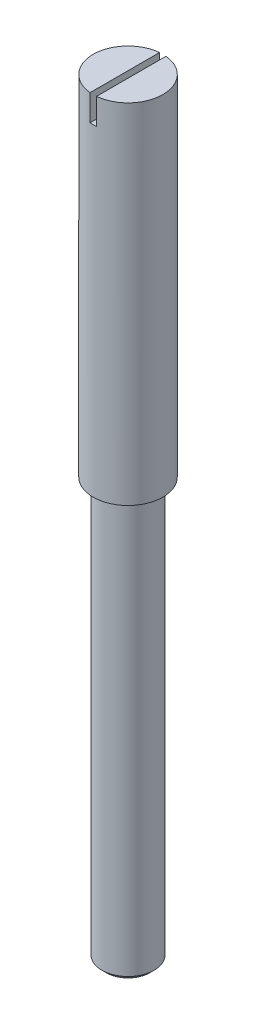
SolidWorks part; units mm, degrees
material "Plain Carbon Steel"
ref_plane "Front Plane" through (0, 0, 0) normal (0, 0, 1) x (1, 0, 0)
ref_plane "Top Plane" through (0, 0, 0) normal (0, 1, 0) x (1, 0, 0)
ref_plane "Right Plane" through (0, 0, 0) normal (1, 0, 0) x (0, 0, -1)
sketch "Sketch1" plane through (0, 0, 0) normal (0, 0, 1) x (1, 0, 0)
  line L0 (0, -1.4901) -> (0, 11.5997) construction
  line L1 (0, 0) -> (0.375, 0)
  line L2 (0.375, 0) -> (0.375, 6)
  line L3 (0.375, 6) -> (0.5, 6)
  line L4 (0.5, 6) -> (0.5, 11)
  line L5 (0.5, 11) -> (0, 11)
  line L6 (0, 0) -> (0, 11)
  dimension "D1" = 11
  dimension "D2" = 5
  dimension "D3" = 0.375
  dimension "D4" = 0.5
revolve "Revolve1" add sketch "Sketch1" angle 360 about L0
sketch "Sketch2" plane through (0, 0, 0) normal (0, 0, 1) x (1, 0, 0)
  line L0 (0.5, 11) -> (-0.5, 11) construction
  line L1 (-0.0465, 11.3483) -> (0.0465, 11.3483)
  line L2 (-0.0465, 11.3483) -> (-0.0465, 10.6257)
  line L3 (-0.0465, 10.6257) -> (0.0465, 10.6257)
  line L4 (0.0465, 11.3483) -> (0.0465, 10.6257)
  point P4 (0, 10.6257)
  dimension "D1" = 0.093
  dimension "D2" = 0.3743
extrude "Cut-Extrude1" cut sketch "Sketch2" against normal through all both and the other way through all
chamfer "Chamfer1" distance 0.062 angle 45 1 edges at (0, 0, -0.375)
